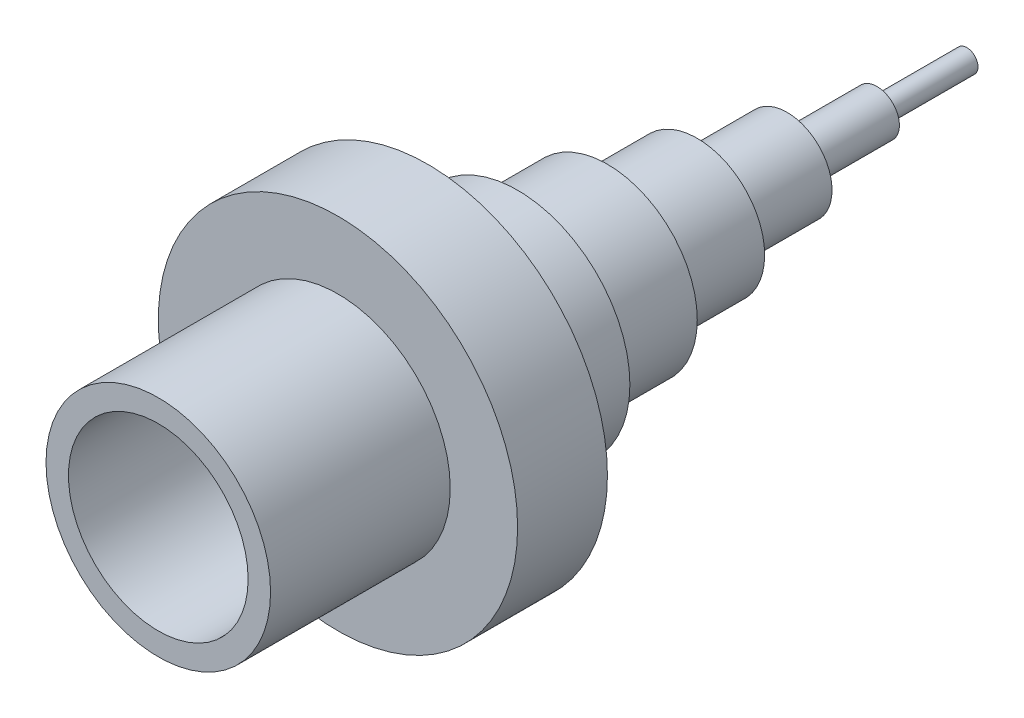
SolidWorks part; units mm, degrees
ref_plane "Alzado" through (0, 0, 0) normal (0, 0, 1) x (1, 0, 0)
ref_plane "Planta" through (0, 0, 0) normal (0, 1, 0) x (1, 0, 0)
ref_plane "Vista lateral" through (0, 0, 0) normal (1, 0, 0) x (0, 0, -1)
sketch "Croquis1" plane through (0, 0, 0) normal (1, 0, 0) x (0, 0, -1)
  line L0 (0, 0) -> (126.1063, 0) construction
  line L2 (0, 25) -> (40, 25)
  line L3 (40, 25) -> (40, 40)
  line L4 (40, 40) -> (60, 40)
  line L5 (60, 40) -> (60, 25)
  line L6 (60, 25) -> (80, 25)
  line L7 (80, 25) -> (80, 20)
  line L8 (80, 20) -> (100, 20)
  line L9 (100, 20) -> (100, 15)
  line L10 (100, 15) -> (120, 15)
  line L11 (120, 15) -> (120, 10)
  line L12 (120, 10) -> (140, 10)
  line L13 (140, 10) -> (140, 5)
  line L14 (140, 5) -> (160, 5)
  line L15 (160, 5) -> (160, 2.5)
  line L16 (160, 2.5) -> (180, 2.5)
  line L17 (180, 2.5) -> (180, 0)
  line L19 (0, 25) -> (0, 20)
  line L20 (0, 20) -> (40, 20)
  line L21 (40, 20) -> (40, 0)
  line L22 (40, 0) -> (180, 0)
  point P21 (22.7205, 20)
  point P24 (77.1469, 30.8866)
  point P25 (80, 30.8866)
  dimension "D1" = 180
  dimension "D2" = 50
  dimension "D3" = 40
  dimension "D4" = 40
  dimension "D5" = 80
  dimension "D6" = 20
  dimension "D7" = 5
  dimension "D8" = 10
  dimension "D9" = 20
  dimension "D10" = 30
  dimension "D11" = 40
  dimension "D12" = 50
revolve "Revolución1" add sketch "Croquis1" angle 360 about L0
equation "\"A\" = 10mm"
equation "\"D1@Croquis1\"=\"A\"*18"
equation "\"D2@Croquis1\"=\"A\"*5"
equation "\"D3@Croquis1\"=\"A\"*4"
equation "\"D4@Croquis1\"=\"A\"*4"
equation "\"D5@Croquis1\"=\"A\"*8"
equation "\"D6@Croquis1\"=\"A\"*2"
equation "\"D7@Croquis1\"=\"A\"/2"
equation "\"D8@Croquis1\"=\"A\""
equation "\"D9@Croquis1\"=\"A\"*2"
equation "\"D10@Croquis1\"=\"A\"*3"
equation "\"D11@Croquis1\"=\"A\"*4"
equation "\"D12@Croquis1\"=\"A\"*5"
